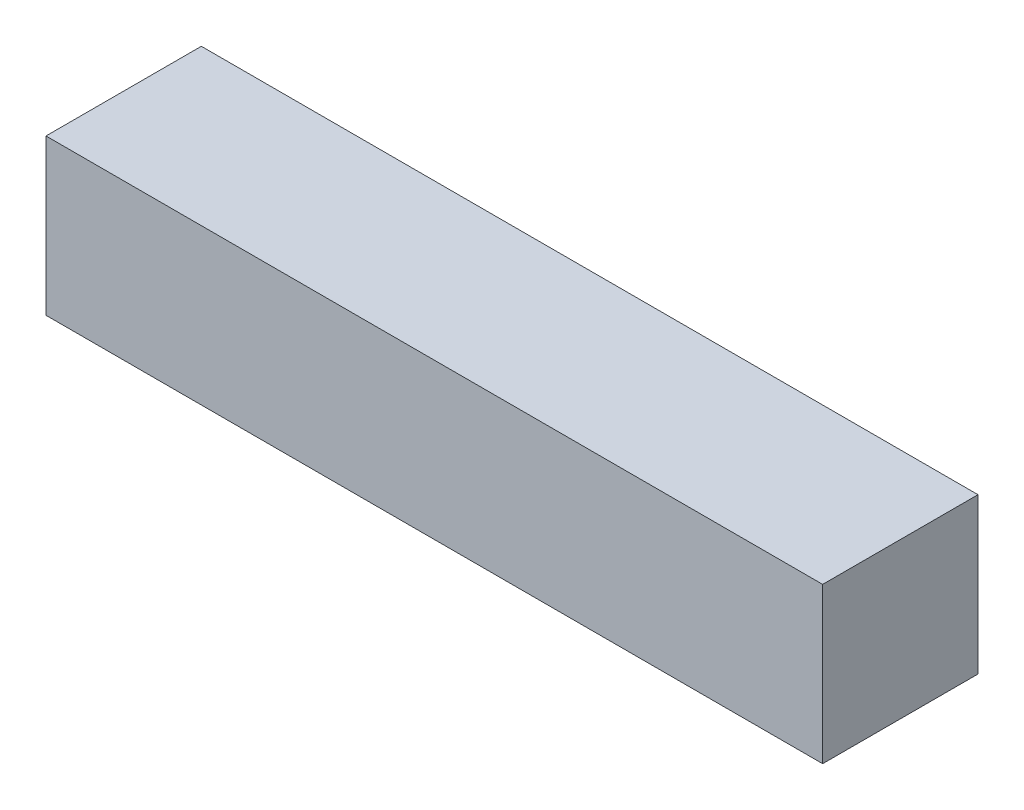
SolidWorks part; units mm, degrees
ref_plane "Front Plane" through (0, 0, 0) normal (0, 0, 1) x (1, 0, 0)
ref_plane "Top Plane" through (0, 0, 0) normal (0, 1, 0) x (1, 0, 0)
ref_plane "Right Plane" through (0, 0, 0) normal (1, 0, 0) x (0, 0, -1)
sketch "Sketch1" plane through (0, 0, 0) normal (0, 1, 0) x (1, 0, 0)
  line L1 (-127, 25.4) -> (127, 25.4)
  line L2 (-127, 25.4) -> (-127, -25.4)
  line L3 (-127, -25.4) -> (127, -25.4)
  line L4 (127, 25.4) -> (127, -25.4)
  line L5 (-127, 25.4) -> (127, -25.4) construction
  line L6 (-127, -25.4) -> (127, 25.4) construction
  point P0 (0, 0)
  dimension "D1" = 254
  dimension "D2" = 50.8
extrude "Boss-Extrude1" add sketch "Sketch1" along normal blind 50.8
